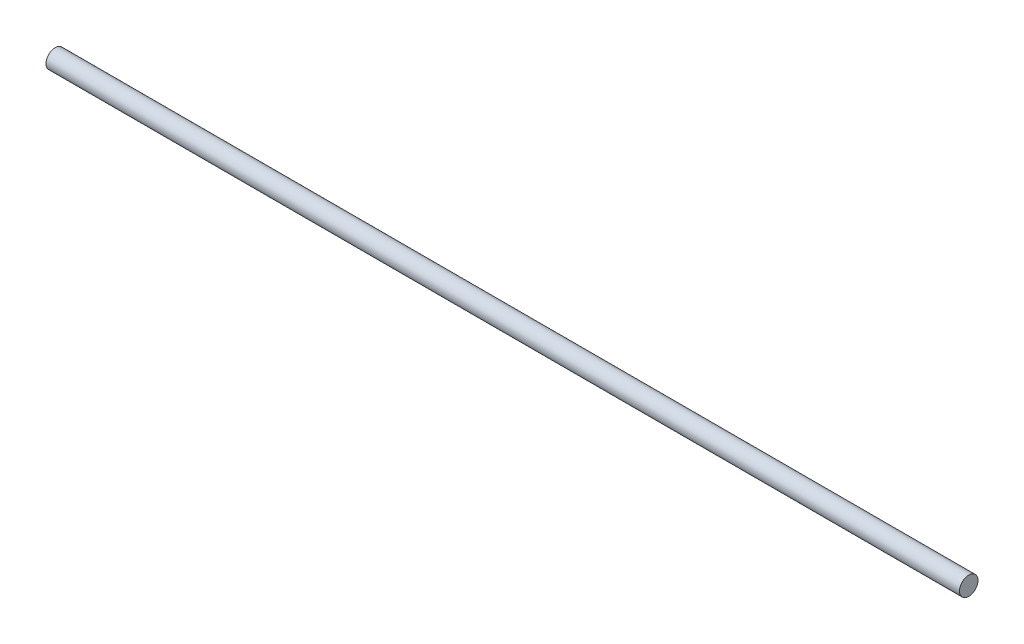
SolidWorks part; units mm, degrees
ref_plane "Alzado" through (0, 0, 0) normal (0, 0, 1) x (1, 0, 0)
ref_plane "Planta" through (0, 0, 0) normal (0, 1, 0) x (1, 0, 0)
ref_plane "Vista lateral" through (0, 0, 0) normal (1, 0, 0) x (0, 0, -1)
sketch "Croquis1" plane through (0, 0, 0) normal (1, 0, 0) x (0, 0, -1)
  circle A0 centre (0, 0) radius 4
  dimension "D1" = 8
extrude "Saliente-Extruir1" add sketch "Croquis1" along normal blind 395.0069
